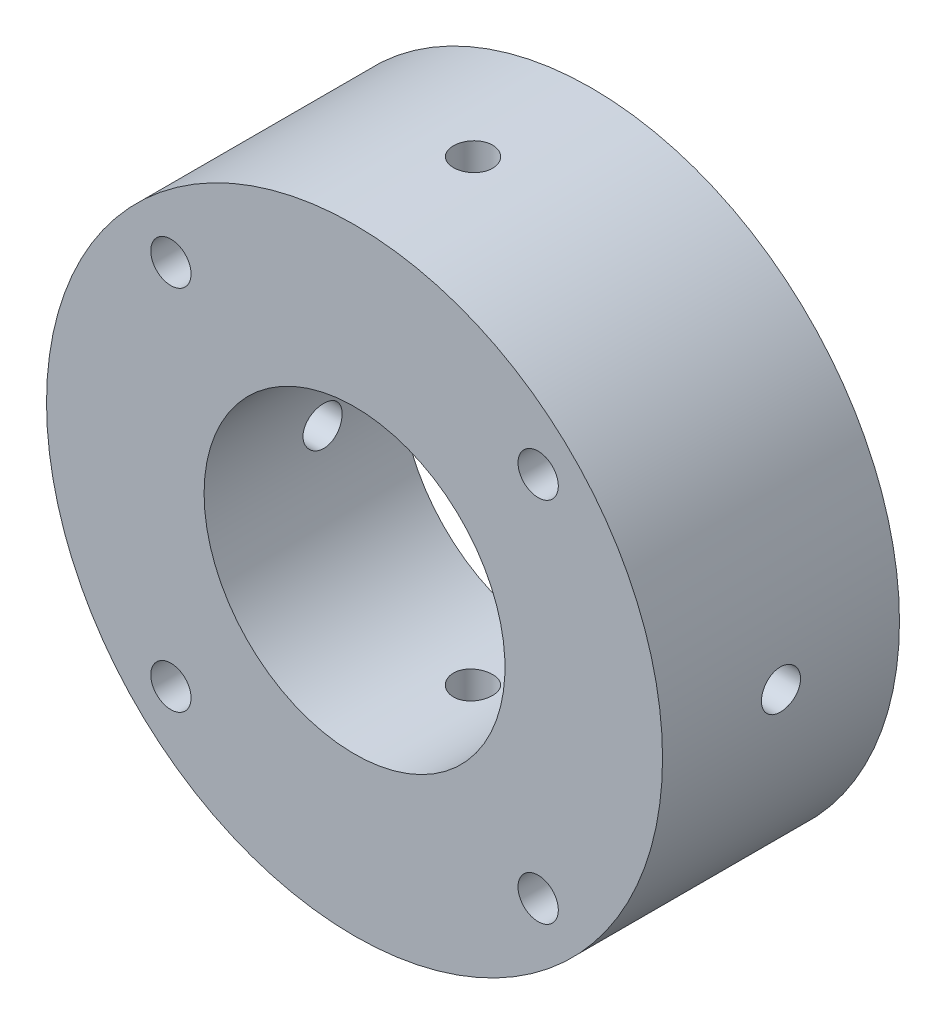
SolidWorks part; units mm, degrees
ref_plane "Front Plane" through (0, 0, 0) normal (0, 0, 1) x (1, 0, 0)
ref_plane "Top Plane" through (0, 0, 0) normal (0, 1, 0) x (1, 0, 0)
ref_plane "Right Plane" through (0, 0, 0) normal (1, 0, 0) x (0, 0, -1)
ref_plane "Plane1" through (0, 0, 0) normal (0, -1, 0) x (1, 0, 0)
sketch "Sketch1" plane through (0, 0, 0) normal (0, -1, 0) x (1, 0, 0)
  line L0 (26, 20) -> (0, 20)
  line L1 (0, 20) -> (0, 0)
  line L2 (0, 0) -> (26, 0)
  line L3 (26, 0) -> (26, 20)
  line L4 (0, 20) -> (0, 0) construction
revolve "Revolve1" add sketch "Sketch1" angle 360 about L4
hole_wizard "#2 Clearance Hole1" positions "Sketch3" profile "Sketch2" hole size "#2" standard "ANSI Inch"
sketch "Sketch3" plane through (0, 0, 0) normal (0, 0, -1) x (-1, 0, 0)
  point P0 (-22.7762, 3.201)
sketch "Sketch2" plane through (22.7762, 3.201, 0) normal (1, 0, 0) x (0, 1, 0)
  line L0 (0, 0) -> (0, 6)
  line L1 (0, 6) -> (1.25, 6)
  line L2 (1.25, 6) -> (1.25, 0)
  line L5 (1.25, 0) -> (0, 0)
  line L10 (0, 6) -> (-1.25, 6) construction
  line L11 (0, -6.35) -> (0, 107.95) construction
  dimension "Hole Dia." = 2.5
  dimension "Hole Depth" = 6
  dimension "Drill Angle" = 180
hole_wizard "Hole1" positions "Sketch5" profile "Sketch4" legacy
sketch "Sketch5" plane through (0, 0, 0) normal (0, 0, -1) x (-1, 0, 0)
  point P0 (0, 0)
sketch "Sketch4" plane through (0, 0, 0) normal (1, 0, 0) x (0, 1, 0)
  line L0 (0, 0) -> (0, 20)
  line L1 (0, 20) -> (12.7, 20)
  line L2 (12.7, 20) -> (12.7, 3.4)
  line L3 (12.7, 3.4) -> (20, 3.4)
  line L4 (20, 3.4) -> (20, 0)
  line L5 (20, 0) -> (0, 0)
  line L6 (0, 110) -> (0, -10) construction
  dimension "Diameter" = 25.4
  dimension "Depth" = 20
  dimension "C-Bore Diameter" = 40
  dimension "C-Bore Depth" = 3.4
hole_wizard "#4 Clearance Hole1" positions "3DSketch1" profile "Sketch6" hole size "#4" standard "ANSI Inch"
sketch3d "3DSketch1"
  point P0 (26, 0, 10)
sketch "Sketch6" plane through (26, 0, 10) normal (0, 1, 0) x (0, 0, -1)
  line L0 (0, 0) -> (0, 65.4076)
  line L1 (0, 65.4076) -> (1.65, 65.4076)
  line L2 (1.65, 65.4076) -> (1.65, 0)
  line L5 (1.65, 0) -> (0, 0)
  line L10 (0, 65.4076) -> (-1.65, 65.4076) construction
  line L11 (0, -6.35) -> (0, 107.95) construction
  dimension "Hole Dia." = 3.3
  dimension "Hole Depth" = 65.4076
  dimension "Drill Angle" = 180
ref_plane "Plane2" through (0, 12.5924, 0) normal (0, -1, 0) x (-1, 0, 0)
hole_wizard "#4 Clearance Hole2" positions "Sketch8" profile "Sketch7" hole size "#4" standard "ANSI Inch"
sketch "Sketch8" plane through (0, 12.5924, 0) normal (0, -1, 0) x (-1, 0, 0)
  point P0 (0, -10)
sketch "Sketch7" plane through (0, 12.5924, 10) normal (1, 0, 0) x (0, 0, -1)
  line L0 (0, 0) -> (0, 13.4076)
  line L1 (0, 13.4076) -> (1.65, 13.4076)
  line L2 (1.65, 13.4076) -> (1.65, 0)
  line L5 (1.65, 0) -> (0, 0)
  line L11 (0, -6.35) -> (0, 107.95) construction
  dimension "Thru Hole Dia." = 3.3
  dimension "Thru Hole Depth" = 13.4076
ref_plane "Plane3" through (0, -12.5924, 0) normal (0, 1, 0) x (1, 0, 0)
hole_wizard "#4 Clearance Hole3" positions "Sketch10" profile "Sketch9" hole size "#4" standard "ANSI Inch"
sketch "Sketch10" plane through (0, -12.5924, 0) normal (0, 1, 0) x (1, 0, 0)
  point P0 (0, -10)
sketch "Sketch9" plane through (0, -12.5924, 10) normal (1, 0, 0) x (0, 0, 1)
  line L0 (0, 0) -> (0, 13.4076)
  line L1 (0, 13.4076) -> (1.65, 13.4076)
  line L2 (1.65, 13.4076) -> (1.65, 0)
  line L5 (1.65, 0) -> (0, 0)
  line L11 (0, -6.35) -> (0, 107.95) construction
  dimension "Thru Hole Dia." = 3.3
  dimension "Thru Hole Depth" = 13.4076
hole_wizard "CBORE for #4 Binding Head Machine Screw1" positions "Sketch12" profile "Sketch11" counterbore size "#4" standard "ANSI Inch"
sketch "Sketch12" plane through (0, 0, 0) normal (0, 0, -1) x (-1, 0, 0)
  point P0 (-15.5, -15.5)
  point P1 (15.5, -15.5)
  point P2 (15.5, 15.5)
  point P3 (-15.5, 15.5)
sketch "Sketch11" plane through (15.5, -15.5, 0) normal (1, 0, 0) x (0, 1, 0)
  line L0 (0, 0) -> (0, 20)
  line L1 (0, 20) -> (1.7, 20)
  line L3 (1.7, 20) -> (1.7, 7.5)
  line L4 (1.7, 7.5) -> (3.25, 7.5)
  line L5 (3.25, 7.5) -> (3.25, 0)
  line L7 (3.25, 0) -> (0, 0)
  line L11 (0, -6.35) -> (0, 107.95) construction
  dimension "Thru Hole Dia." = 3.4
  dimension "Thru Hole Depth" = 20
  dimension "C'Bore Dia." = 6.5
  dimension "C'Bore Depth" = 7.5
